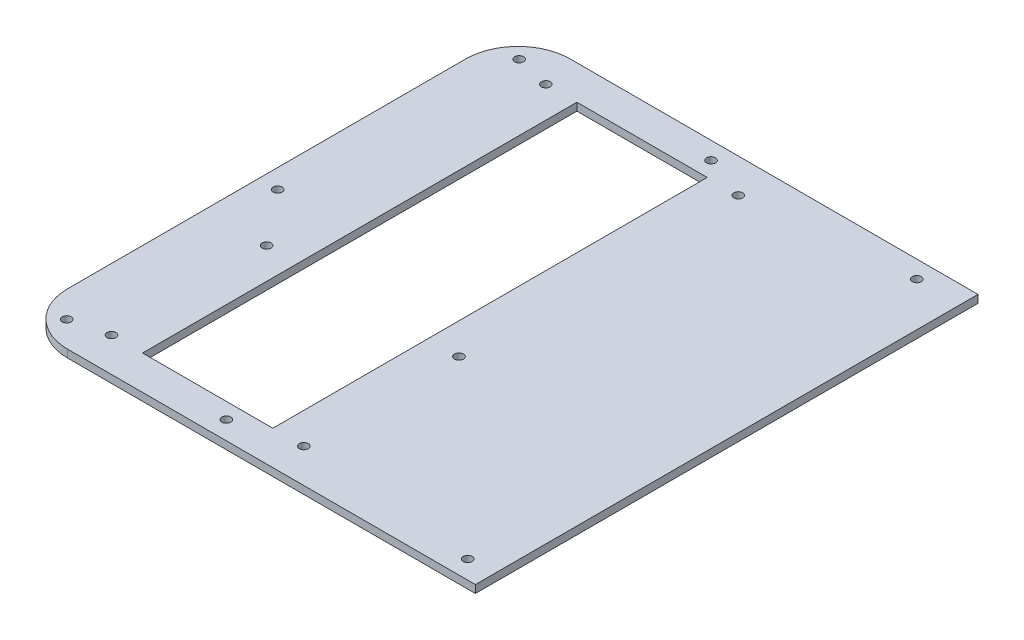
SolidWorks part; units mm, degrees
ref_plane "Front Plane" through (0, 0, 0) normal (0, 0, 1) x (1, 0, 0)
ref_plane "Top Plane" through (0, 0, 0) normal (0, 1, 0) x (1, 0, 0)
ref_plane "Right Plane" through (0, 0, 0) normal (1, 0, 0) x (0, 0, -1)
sketch "Sketch2" plane through (0, 0, 0) normal (0, 1, 0) x (1, 0, 0)
  line L0 (-188.9301, 0) -> (219.0756, 0) construction
  line L9 (-106.934, -102.87) -> (106.934, -102.87)
  line L10 (-128.27, -81.534) -> (-128.27, 81.534)
  line L11 (-106.934, 102.87) -> (106.934, 102.87)
  line L12 (128.27, -81.534) -> (128.27, 81.534)
  line L13 (0, 136.8504) -> (0, -187.3302) construction
  arc A4 (-106.934, -102.87) -> (-128.27, -81.534) centre (-106.934, -81.534) cw
  arc A5 (106.934, -102.87) -> (128.27, -81.534) centre (106.934, -81.534) ccw
  arc A6 (106.934, 102.87) -> (128.27, 81.534) centre (106.934, 81.534) cw
  arc A7 (-128.27, 81.534) -> (-106.934, 102.87) centre (-106.934, 81.534) cw
  point P9 (128.27, 0)
  point P10 (0, 102.87)
  point P13 (-128.27, -102.87)
  point P18 (128.27, 102.87)
  point P21 (-128.27, 102.87)
  dimension "D3" = 128.27
  dimension "D4" = 21.336
  dimension "D1" = 256.54
  dimension "D2" = 205.74
extrude "Boss-Extrude1" add sketch "Sketch2" along normal blind 3.175
sketch "Sketch3" plane through (0, 0, 0) normal (0, 1, 0) x (1, 0, 0)
  line L7 (-90.17, 88.9) -> (-36.83, 88.9)
  line L8 (-90.17, 88.9) -> (-90.17, -88.9)
  line L9 (-90.17, -88.9) -> (-36.83, -88.9)
  line L10 (-36.83, 88.9) -> (-36.83, -88.9)
  line L11 (-90.17, 88.9) -> (-36.83, -88.9) construction
  line L12 (-90.17, -88.9) -> (-36.83, 88.9) construction
  point P5 (-63.5, 0)
  point P6 (0, 0)
  dimension "D1" = 63.5
  dimension "D2" = 177.8
  dimension "D4" = 53.34
extrude "Cut-Extrude1" cut sketch "Sketch3" along normal blind 3.175
hole_wizard "#27 (0.144) Diameter Hole2" positions "Sketch8" profile "Sketch9" hole size "#27" standard "ANSI Inch" end condition through all
sketch "Sketch8" plane through (0, 3.175, 0) normal (0, 1, 0) x (1, 0, 0)
  line L6 (-102.87, -88.9) -> (-102.87, -25.4) construction
  line L8 (-102.87, -88.9) -> (-90.17, -88.9) construction
  line L12 (-63.5, 88.9) -> (-63.5, -88.9) construction
  line L13 (-36.83, 88.9) -> (-90.17, 88.9) construction
  line L14 (-90.17, -88.9) -> (-36.83, -88.9) construction
  line L16 (-90.17, 88.9) -> (-102.87, 88.9) construction
  line L18 (-36.83, 88.9) -> (-24.13, 88.9) construction
  line L20 (-90.17, 88.9) -> (-90.17, -88.9) construction
  line L21 (-24.13, -88.9) -> (-36.83, -88.9) construction
  line L22 (-24.13, -88.9) -> (-24.13, -25.4) construction
  point P0 (-24.13, -25.4)
  point P2 (-24.13, 88.9)
  point P4 (-102.87, 88.9)
  point P6 (-102.87, -25.4)
  point P32 (-102.87, -88.9)
  point P71 (-24.13, -88.9)
  point P74 (0, 0)
  dimension "D1" = 12.7
  dimension "D2" = 12.7
  dimension "D3" = 63.5
sketch "Sketch9" plane through (-24.13, 3.175, 25.4) normal (1, 0, 0) x (0, 0, 1)
  line L0 (0, 0) -> (0, 3.175)
  line L1 (0, 3.175) -> (1.8288, 3.175)
  line L2 (1.8288, 3.175) -> (1.8288, 0)
  line L5 (1.8288, 0) -> (0, 0)
  line L11 (0, -6.35) -> (0, 107.95) construction
  dimension "Thru Hole Dia." = 3.6576
  dimension "Thru Hole Depth" = 3.175
sketch "Sketch10" plane through (0, 3.175, 0) normal (0, 1, 0) x (1, 0, 0)
  line L0 (0, 0) -> (0, 207.7092) construction
  line L1 (-106.7689, -102.8065) -> (106.7689, -102.8065)
  line L2 (-128.2065, -81.3689) -> (-128.2065, 81.3689)
  line L3 (-106.7689, 102.8065) -> (106.7689, 102.8065)
  line L4 (128.2065, -81.3689) -> (128.2065, 81.3689)
  line L5 (-128.2065, -102.8065) -> (128.2065, 102.8065) construction
  line L6 (-128.2065, 102.8065) -> (128.2065, -102.8065) construction
  line L7 (0, 207.7092) -> (0, -151.1165) construction
  arc A0 (-106.7689, -102.8065) -> (-128.2065, -81.3689) centre (-106.7689, -81.3689) cw
  arc A1 (106.7689, -102.8065) -> (128.2065, -81.3689) centre (106.7689, -81.3689) ccw
  arc A2 (106.7689, 102.8065) -> (128.2065, 81.3689) centre (106.7689, 81.3689) cw
  arc A3 (-128.2065, 81.3689) -> (-106.7689, 102.8065) centre (-106.7689, 81.3689) cw
  circle A4 centre (42.1132, 95.7453) radius 2.7813
  circle A5 centre (117.221, 92.2909) radius 2.7813
  circle A6 centre (120.4468, -3.3147) radius 2.7813
  circle A7 centre (117.6274, -92.5195) radius 2.7813
  circle A8 centre (49.403, -95.3643) radius 2.7813
  circle A9 centre (-49.403, -95.3643) radius 2.7813
  circle A10 centre (-117.6274, -92.5195) radius 2.7813
  circle A11 centre (-120.4468, -3.3147) radius 2.7813
  circle A12 centre (-117.221, 92.2909) radius 2.7813
  circle A13 centre (-42.1132, 95.7453) radius 2.7813
  point P0 (0, 0)
  point P5 (42.1132, 95.7453)
  point P22 (117.221, 92.2909)
  point P24 (117.6274, -92.5195)
  point P26 (49.403, -95.3643)
  point P27 (120.4468, -3.3147)
  point P30 (-49.403, -95.3643)
  point P32 (-117.6274, -92.5195)
  point P34 (-120.4468, -3.3147)
  point P36 (-117.221, 92.2909)
  point P38 (-42.1132, 95.7453)
  dimension "D3" = 21.4376
  dimension "D4" = 5.5626
  dimension "D7" = 5.5626
  dimension "D10" = 5.5626
  dimension "D13" = 5.5626
  dimension "D16" = 5.5626
  dimension "D1" = 205.613
  dimension "D2" = 256.413
  dimension "D5" = 42.1132
  dimension "D6" = 7.0612
  dimension "D8" = 117.221
  dimension "D9" = 10.5156
  dimension "D11" = 120.4468
  dimension "D12" = 106.1212
  dimension "D14" = 195.326
  dimension "D15" = 117.6274
  dimension "D17" = 7.4422
  dimension "D18" = 49.403
hole_wizard "#27 (0.144) Diameter Hole3" positions "Sketch10" profile "Sketch11" hole size "#27" standard "ANSI Inch"
sketch "Sketch11" plane through (-42.1132, 3.175, -95.7453) normal (1, 0, 0) x (0, 0, 1)
  line L0 (0, 0) -> (0, 3.175)
  line L1 (0, 3.175) -> (1.8288, 3.175)
  line L2 (1.8288, 3.175) -> (1.8288, 0)
  line L5 (1.8288, 0) -> (0, 0)
  line L11 (0, -6.35) -> (0, 107.95) construction
  dimension "Thru Hole Dia." = 3.6576
  dimension "Thru Hole Depth" = 3.175
sketch "Sketch12" plane through (0, 3.175, 0) normal (0, 1, 0) x (1, 0, 0)
  line L0 (49.403, -95.3643) -> (60.0456, -95.3643) construction
  line L1 (60.0456, -127) -> (187.0456, -127)
  line L2 (60.0456, -127) -> (60.0456, 127)
  line L3 (60.0456, 127) -> (187.0456, 127)
  line L4 (187.0456, -127) -> (187.0456, 127)
  line L5 (60.0456, -127) -> (187.0456, 127) construction
  line L6 (60.0456, 127) -> (187.0456, -127) construction
  line L7 (-117.6274, -92.5195) -> (-128.27, -92.5195) construction
  line L9 (-128.27, -73.2292) -> (-128.27, -92.5195) construction
  line L10 (-128.27, 81.534) -> (-128.27, -81.534) construction
  point P0 (123.5456, 0)
  dimension "D1" = 127
  dimension "D2" = 254
extrude "Cut-Extrude2" cut sketch "Sketch12" against normal blind 25.4
sketch "Sketch13" plane through (0, 3.175, 0) normal (0, 1, 0) x (1, 0, 0)
